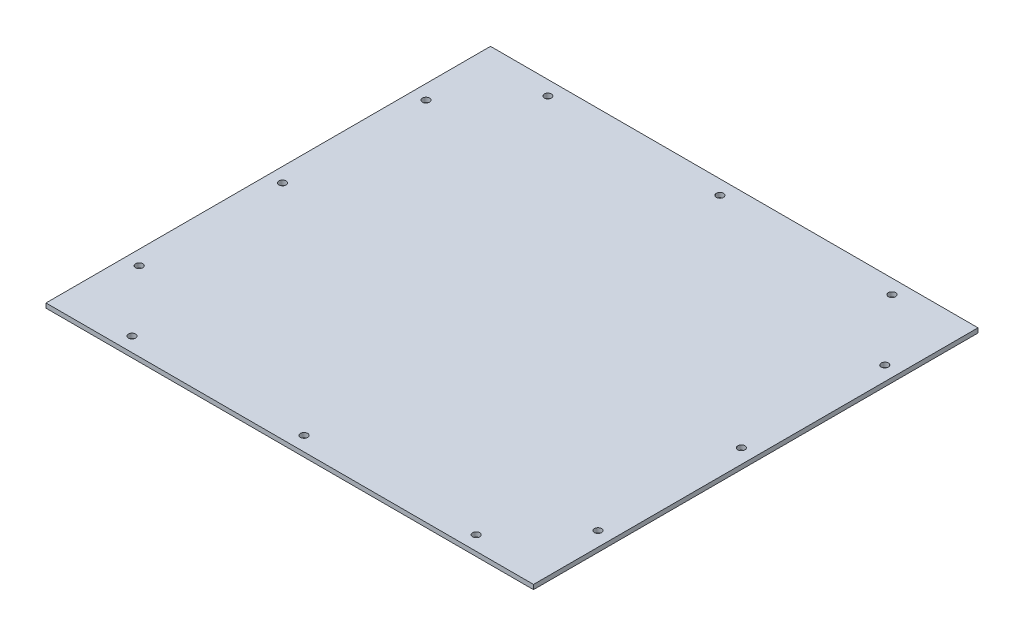
SolidWorks part; units mm, degrees
ref_plane "Front Plane" through (0, 0, 0) normal (0, 0, 1) x (1, 0, 0)
ref_plane "Top Plane" through (0, 0, 0) normal (0, 1, 0) x (1, 0, 0)
ref_plane "Right Plane" through (0, 0, 0) normal (1, 0, 0) x (0, 0, -1)
sketch "Sketch1" plane through (0, 0, 0) normal (0, 1, 0) x (1, 0, 0)
  line L1 (0, 0) -> (340, 0)
  line L2 (0, 0) -> (0, 310)
  line L3 (0, 310) -> (340, 310)
  line L4 (340, 0) -> (340, 310)
  dimension "D1" = 310
  dimension "D2" = 340
extrude "Boss-Extrude1" add sketch "Sketch1" along normal blind 3.175
sketch "Sketch2" plane through (0, 3.175, 0) normal (0, 1, 0) x (1, 0, 0)
  line L0 (0, 310) -> (0, 0) construction
  line L1 (340, 310) -> (0, 310) construction
  line L2 (340, 0) -> (340, 310) construction
  line L3 (0, 0) -> (340, 0) construction
  circle A0 centre (10, 155) radius 2.5
  circle A1 centre (10, 255) radius 2.5
  circle A2 centre (10, 55) radius 2.5
  circle A3 centre (50, 10) radius 2.5
  circle A4 centre (170, 10) radius 2.5
  circle A5 centre (290, 10) radius 2.5
  circle A6 centre (330, 55) radius 2.5
  circle A7 centre (330, 155) radius 2.5
  circle A8 centre (330, 255) radius 2.5
  circle A9 centre (290, 300) radius 2.5
  circle A10 centre (170, 300) radius 2.5
  circle A11 centre (50, 300) radius 2.5
  point P33 (0, 0)
  dimension "D1" = 5
  dimension "D2" = 10
  dimension "D3" = 10
  dimension "D6" = 10
  dimension "D7" = 10
  dimension "D8" = 10
  dimension "D9" = 10
  dimension "D10" = 10
  dimension "D11" = 10
  dimension "D12" = 10
  dimension "D13" = 10
  dimension "D14" = 170
  dimension "D15" = 170
  dimension "D16" = 155
  dimension "D19" = 120
  dimension "D22" = 120
  dimension "D23" = 120
  dimension "D24" = 100
  dimension "D25" = 100
  dimension "D4" = 10
  dimension "D5" = 10
  dimension "D17" = 155
  dimension "D18" = 120
  dimension "D20" = 100
  dimension "D21" = 100
extrude "Cut-Extrude1" cut sketch "Sketch2" against normal blind 3.175
